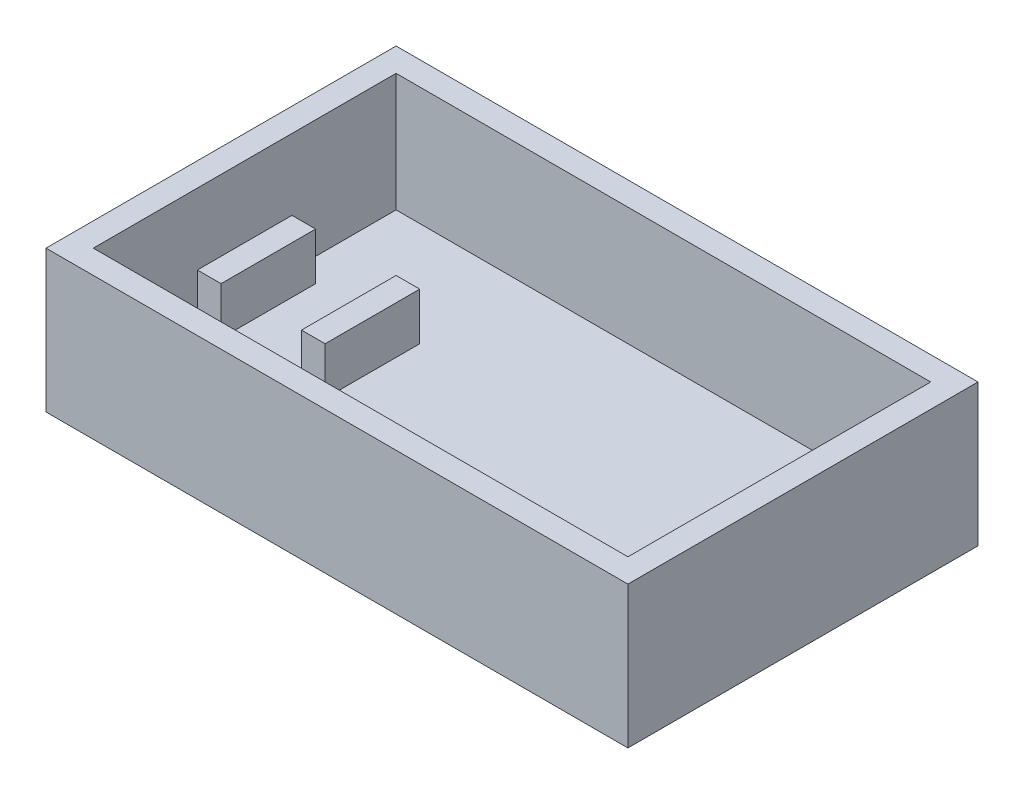
SolidWorks part; units mm, degrees
ref_plane "Front Plane" through (0, 0, 0) normal (0, 0, 1) x (1, 0, 0)
ref_plane "Top Plane" through (0, 0, 0) normal (0, 1, 0) x (1, 0, 0)
ref_plane "Right Plane" through (0, 0, 0) normal (1, 0, 0) x (0, 0, -1)
sketch "Sketch1" plane through (0, 0, 0) normal (0, 1, 0) x (1, 0, 0)
  line L1 (-61.5, 37) -> (61.5, 37)
  line L2 (-61.5, 37) -> (-61.5, -37)
  line L3 (-61.5, -37) -> (61.5, -37)
  line L4 (61.5, 37) -> (61.5, -37)
  line L5 (-61.5, 37) -> (61.5, -37) construction
  line L6 (-61.5, -37) -> (61.5, 37) construction
  point P0 (0, 0)
extrude "Boss-Extrude1" add sketch "Sketch1" along normal blind 30
sketch "Sketch2" plane through (0, 30, 0) normal (0, 1, 0) x (1, 0, 0)
  line L1 (-56.5, 32) -> (56.5, 32)
  line L2 (-56.5, 32) -> (-56.5, -32)
  line L3 (-56.5, -32) -> (56.5, -32)
  line L4 (56.5, 32) -> (56.5, -32)
  line L5 (-56.5, 32) -> (56.5, -32) construction
  line L6 (-56.5, -32) -> (56.5, 32) construction
  point P0 (0, 0)
extrude "Cut-Extrude1" cut sketch "Sketch2" against normal blind 25
sketch "Sketch4" plane through (0, 5, 0) normal (0, 1, 0) x (1, 0, 0)
  line L0 (-56.5, 0) -> (56.5, 0) construction
  line L1 (-56.5, 32) -> (-56.5, -32) construction
  line L2 (56.5, -32) -> (56.5, 32) construction
  line L3 (-56.5, 0) -> (-54, 0)
  line L5 (-51.5, -10) -> (-56.5, -10)
  line L6 (-51.5, -10) -> (-51.5, 10)
  line L7 (-51.5, 10) -> (-56.5, 10)
  line L8 (-56.5, -10) -> (-56.5, 10)
  line L9 (-51.5, -10) -> (-56.5, 10) construction
  line L10 (-51.5, 10) -> (-56.5, -10) construction
extrude "Boss-Extrude2" add sketch "Sketch4" along normal blind 10
pattern_linear "LPattern1" count 2 spacing 22 along (1, 0, 0) of "Boss-Extrude2"
